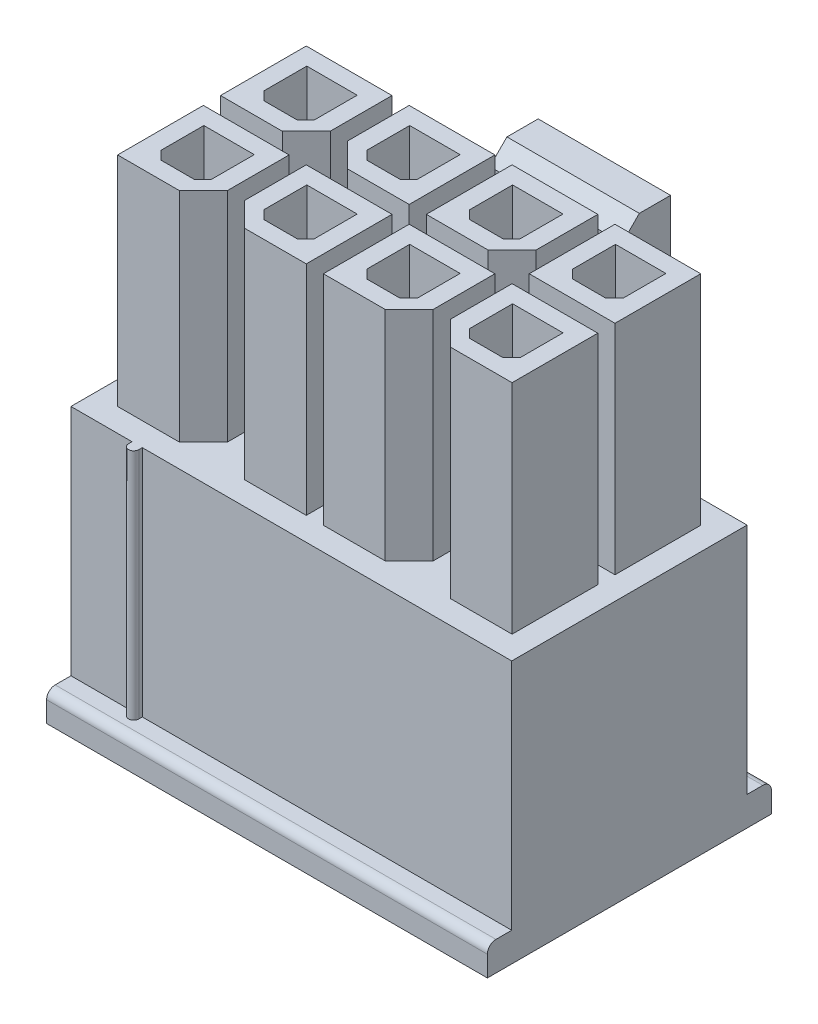
SolidWorks part; units mm, degrees
material "ABS"
ref_plane "Front Plane" through (0, 0, 0) normal (0, 0, 1) x (1, 0, 0)
ref_plane "Top Plane" through (0, 0, 0) normal (0, 1, 0) x (1, 0, 0)
ref_plane "Right Plane" through (0, 0, 0) normal (1, 0, 0) x (0, 0, -1)
ref_plane "Plane1" through (0, 0, 4.14) normal (0, 0, 1) x (1, 0, 0)
sketch "Sketch1" plane through (0, 0, 4.14) normal (0, 0, 1) x (1, 0, 0)
  line L0 (-6.43, -4) -> (6.42, -4)
  line L1 (6.42, -4) -> (6.42, 3.65)
  line L2 (6.42, 3.65) -> (-6.43, 3.65)
  line L3 (-6.43, 3.65) -> (-6.43, -4)
extrude "Boss-Extrude1" add sketch "Sketch1" against normal blind 7.57
sketch "Sketch2" plane through (0, 0, -3.43) normal (0, 0, -1) x (-1, 0, 0)
  line L0 (1.93, 1.6) -> (-1.93, 1.6)
  line L1 (-1.93, 1.6) -> (-1.93, 2.51)
  line L2 (-1.93, 2.51) -> (1.93, 2.51)
  line L3 (1.93, 2.51) -> (1.93, 1.6)
extrude "Boss-Extrude2" add sketch "Sketch2" along normal blind 3.28
sketch "Sketch3" plane through (0, 2.51, 0) normal (0, 1, 0) x (-1, 0, 0)
  line L0 (-1.93, -6.71) -> (-1.93, -4.28)
  line L1 (-1.93, -4.28) -> (1.93, -4.28)
  line L2 (1.93, -4.28) -> (1.93, -6.71)
  line L3 (1.93, -6.71) -> (-1.93, -6.71)
extrude "Boss-Extrude3" add sketch "Sketch3" along normal blind 6.09
sketch "Sketch4" plane through (0, 1.6, 0) normal (0, -1, 0) x (1, 0, 0)
  line L0 (-1.93, -4.28) -> (1.93, -4.28)
  line L1 (1.93, -4.28) -> (1.93, -6.71)
  line L2 (1.93, -6.71) -> (-1.93, -6.71)
  line L3 (-1.93, -6.71) -> (-1.93, -4.28)
extrude "Boss-Extrude4" add sketch "Sketch4" along normal blind 4
sketch "Sketch5" plane through (-1.93, 0, 0) normal (-1, 0, 0) x (0, 0, 1)
  line L0 (-6.71, 8.6) -> (-6.71, -0.9)
  line L1 (-6.71, -0.9) -> (-5.69, -0.9)
  line L2 (-5.69, -0.9) -> (-5.69, 8.6)
  line L3 (-5.69, 8.6) -> (-6.71, 8.6)
extrude "Cut-Extrude1" cut sketch "Sketch5" against normal through all
sketch "Sketch6" plane through (6.42, 0, 0) normal (1, 0, 0) x (0, 0, -1)
  line L0 (-4.14, -3.15) -> (-3.43, -3.15)
  line L1 (-3.43, -3.15) -> (-3.43, 3.65)
  line L2 (-3.43, 3.65) -> (-4.14, 3.65)
  line L3 (-4.14, 3.65) -> (-4.14, -3.15)
extrude "Cut-Extrude2" cut sketch "Sketch6" against normal through all
sketch "Sketch7" plane through (0, -3.15, 0) normal (0, 1, 0) x (-1, 0, 0)
  line L0 (4.35, 3.43) -> (4.35, 3.53)
  line L1 (4.65, 3.53) -> (4.65, 3.43)
  line L2 (4.65, 3.43) -> (4.35, 3.43)
  arc A0 (4.35, 3.53) -> (4.65, 3.53) centre (4.5, 3.53) cw
extrude "Boss-Extrude5" add sketch "Sketch7" along normal blind 6.8
sketch "Sketch8" plane through (0, 0, -3.43) normal (0, 0, -1) x (-1, 0, 0)
  line L0 (-2.73, -4) -> (-6.42, -4)
  line L1 (-6.42, -4) -> (-6.42, -3.15)
  line L2 (-6.42, -3.15) -> (-2.73, -3.15)
  line L3 (-2.73, -3.15) -> (-2.73, -4)
extrude "Boss-Extrude6" add sketch "Sketch8" along normal blind 0.71
sketch "Sketch9" plane through (0, 0, -3.43) normal (0, 0, -1) x (-1, 0, 0)
  line L0 (6.43, -3.15) -> (6.43, -4)
  line L1 (6.43, -4) -> (2.73, -4)
  line L2 (2.73, -4) -> (2.73, -3.15)
  line L3 (2.73, -3.15) -> (6.43, -3.15)
extrude "Boss-Extrude7" add sketch "Sketch9" along normal blind 0.71
sketch "Sketch10" plane through (0, 3.65, 0) normal (0, 1, 0) x (-1, 0, 0)
  line L0 (3.25, -2.75) -> (3.25, -0.25)
  line L1 (3.25, -0.25) -> (5.75, -0.25)
  line L2 (5.75, -0.25) -> (5.75, -2.75)
  line L3 (5.75, -2.75) -> (3.25, -2.75)
extrude "Boss-Extrude8" add sketch "Sketch10" along normal blind 6.35
sketch "Sketch11" plane through (0, 10, 0) normal (0, 1, 0) x (-1, 0, 0)
  line L0 (3.765, -0.75) -> (3.765, -2.25)
  line L1 (3.765, -2.25) -> (5.235, -2.25)
  line L2 (5.235, -2.25) -> (5.235, -0.75)
  line L3 (5.235, -0.75) -> (3.765, -0.75)
extrude "Cut-Extrude3" cut sketch "Sketch11" against normal blind 5.8
sketch "Sketch12" plane through (0, 3.65, 0) normal (0, 1, 0) x (-1, 0, 0)
  line L0 (3.25, 0.25) -> (3.25, 2.75)
  line L1 (3.25, 2.75) -> (5.75, 2.75)
  line L2 (5.75, 2.75) -> (5.75, 0.25)
  line L3 (5.75, 0.25) -> (3.25, 0.25)
extrude "Boss-Extrude9" add sketch "Sketch12" along normal blind 6.35
sketch "Sketch13" plane through (0, 10, 0) normal (0, 1, 0) x (-1, 0, 0)
  line L0 (3.765, 2.25) -> (3.765, 0.75)
  line L1 (3.765, 0.75) -> (5.235, 0.75)
  line L2 (5.235, 0.75) -> (5.235, 2.25)
  line L3 (5.235, 2.25) -> (3.765, 2.25)
extrude "Cut-Extrude4" cut sketch "Sketch13" against normal blind 5.8
sketch "Sketch14" plane through (0, 3.65, 0) normal (0, 1, 0) x (-1, 0, 0)
  line L0 (0.25, 2.75) -> (2.75, 2.75)
  line L1 (2.75, 2.75) -> (2.75, 0.25)
  line L2 (2.75, 0.25) -> (0.25, 0.25)
  line L3 (0.25, 0.25) -> (0.25, 2.75)
extrude "Boss-Extrude10" add sketch "Sketch14" along normal blind 6.35
sketch "Sketch15" plane through (0, 10, 0) normal (0, 1, 0) x (-1, 0, 0)
  line L0 (0.765, 2.25) -> (0.765, 0.75)
  line L1 (0.765, 0.75) -> (2.235, 0.75)
  line L2 (2.235, 0.75) -> (2.235, 2.25)
  line L3 (2.235, 2.25) -> (0.765, 2.25)
extrude "Cut-Extrude5" cut sketch "Sketch15" against normal blind 5.8
sketch "Sketch16" plane through (0, 3.65, 0) normal (0, 1, 0) x (-1, 0, 0)
  line L0 (0.25, -0.25) -> (2.75, -0.25)
  line L1 (2.75, -0.25) -> (2.75, -2.75)
  line L2 (2.75, -2.75) -> (0.25, -2.75)
  line L3 (0.25, -2.75) -> (0.25, -0.25)
extrude "Boss-Extrude11" add sketch "Sketch16" along normal blind 6.35
sketch "Sketch17" plane through (0, 10, 0) normal (0, 1, 0) x (-1, 0, 0)
  line L0 (0.765, -0.75) -> (0.765, -2.25)
  line L1 (0.765, -2.25) -> (2.235, -2.25)
  line L2 (2.235, -2.25) -> (2.235, -0.75)
  line L3 (2.235, -0.75) -> (0.765, -0.75)
extrude "Cut-Extrude6" cut sketch "Sketch17" against normal blind 5.8
sketch "Sketch18" plane through (0, 3.65, 0) normal (0, 1, 0) x (-1, 0, 0)
  line L0 (-2.75, -2.75) -> (-2.75, -0.25)
  line L1 (-2.75, -0.25) -> (-0.25, -0.25)
  line L2 (-0.25, -0.25) -> (-0.25, -2.75)
  line L3 (-0.25, -2.75) -> (-2.75, -2.75)
extrude "Boss-Extrude12" add sketch "Sketch18" along normal blind 6.35
sketch "Sketch19" plane through (0, 10, 0) normal (0, 1, 0) x (-1, 0, 0)
  line L0 (-2.235, -0.75) -> (-2.235, -2.25)
  line L1 (-2.235, -2.25) -> (-0.765, -2.25)
  line L2 (-0.765, -2.25) -> (-0.765, -0.75)
  line L3 (-0.765, -0.75) -> (-2.235, -0.75)
extrude "Cut-Extrude7" cut sketch "Sketch19" against normal blind 5.8
sketch "Sketch20" plane through (0, 3.65, 0) normal (0, 1, 0) x (-1, 0, 0)
  line L0 (-2.75, 0.25) -> (-2.75, 2.75)
  line L1 (-2.75, 2.75) -> (-0.25, 2.75)
  line L2 (-0.25, 2.75) -> (-0.25, 0.25)
  line L3 (-0.25, 0.25) -> (-2.75, 0.25)
extrude "Boss-Extrude13" add sketch "Sketch20" along normal blind 6.35
sketch "Sketch21" plane through (0, 10, 0) normal (0, 1, 0) x (-1, 0, 0)
  line L0 (-2.235, 2.25) -> (-2.235, 0.75)
  line L1 (-2.235, 0.75) -> (-0.765, 0.75)
  line L2 (-0.765, 0.75) -> (-0.765, 2.25)
  line L3 (-0.765, 2.25) -> (-2.235, 2.25)
extrude "Cut-Extrude8" cut sketch "Sketch21" against normal blind 5.8
sketch "Sketch22" plane through (0, 3.65, 0) normal (0, 1, 0) x (-1, 0, 0)
  line L0 (-5.75, 2.75) -> (-3.25, 2.75)
  line L1 (-3.25, 2.75) -> (-3.25, 0.25)
  line L2 (-3.25, 0.25) -> (-5.75, 0.25)
  line L3 (-5.75, 0.25) -> (-5.75, 2.75)
extrude "Boss-Extrude14" add sketch "Sketch22" along normal blind 6.35
sketch "Sketch23" plane through (0, 10, 0) normal (0, 1, 0) x (-1, 0, 0)
  line L0 (-5.235, 2.25) -> (-5.235, 0.75)
  line L1 (-5.235, 0.75) -> (-3.765, 0.75)
  line L2 (-3.765, 0.75) -> (-3.765, 2.25)
  line L3 (-3.765, 2.25) -> (-5.235, 2.25)
extrude "Cut-Extrude9" cut sketch "Sketch23" against normal blind 5.8
sketch "Sketch24" plane through (0, 3.65, 0) normal (0, 1, 0) x (-1, 0, 0)
  line L0 (-3.25, -2.75) -> (-5.75, -2.75)
  line L1 (-5.75, -2.75) -> (-5.75, -0.25)
  line L2 (-5.75, -0.25) -> (-3.25, -0.25)
  line L3 (-3.25, -0.25) -> (-3.25, -2.75)
extrude "Boss-Extrude15" add sketch "Sketch24" along normal blind 6.35
sketch "Sketch25" plane through (0, 10, 0) normal (0, 1, 0) x (-1, 0, 0)
  line L0 (-5.235, -0.75) -> (-5.235, -2.25)
  line L1 (-5.235, -2.25) -> (-3.765, -2.25)
  line L2 (-3.765, -2.25) -> (-3.765, -0.75)
  line L3 (-3.765, -0.75) -> (-5.235, -0.75)
extrude "Cut-Extrude10" cut sketch "Sketch25" against normal blind 5.8
draft "Draft1" type of draft neutral plane draft angle 36.327 faces to draft 1 face at (0, -0.9, -6.2) neutral plane through (6.42, -0.9, -5.69) neutral plane normal (0, 0, -1) parameters "D1"=36.327
chamfer "Chamfer1" distance 0.25 angle 45 16 edges at (-0.765, 7.1, 2.25) (2.235, 7.1, -0.75) (0.765, 7.1, -0.75) (-5.235, 7.1, 2.25) (2.235, 7.1, 2.25) (-0.765, 7.1, -0.75) (0.765, 7.1, 2.25) (5.235, 7.1, 2.25) (3.765, 7.1, 2.25) (-3.765, 7.1, -0.75) (-3.765, 7.1, 2.25) (-5.235, 7.1, -0.75) (-2.235, 7.1, 2.25) (-2.235, 7.1, -0.75) (5.235, 7.1, -0.75) (3.765, 7.1, -0.75)
chamfer "Chamfer2" distance 0.7 angle 45 7 edges at (2.75, 6.825, 2.75) (-3.25, 6.825, 2.75) (-2.75, 6.825, -0.25) (-2.75, 6.825, 2.75) (2.75, 6.825, -0.25) (3.25, 6.825, 2.75) (-3.25, 6.825, -0.25)
chamfer "Chamfer3" distance 0.5 angle 45 1 edges at (0, 8.6, -4.28)
fillet "Fillet1" radius 0.25 5 edges at (-0.005, -3.15, 4.14) (4.575, -3.15, -4.14) (-4.58, -3.15, -4.14) (-1.93, 2.055, -3.43) (1.93, 2.055, -3.43)
fillet "Fillet2" radius 0.5 2 edges at (0, 1.6, -4.28) (0, 2.51, -4.28)
